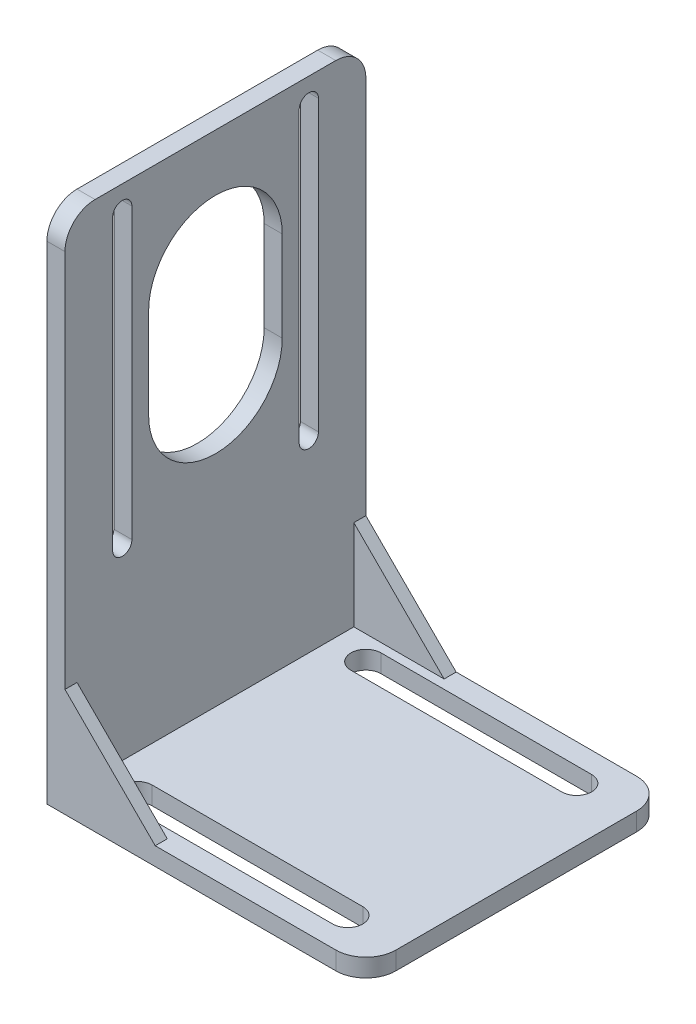
SolidWorks part; units mm, degrees
ref_plane "前视基准面" through (0, 0, 0) normal (0, 0, 1) x (1, 0, 0)
ref_plane "上视基准面" through (0, 0, 0) normal (0, 1, 0) x (1, 0, 0)
ref_plane "右视基准面" through (0, 0, 0) normal (1, 0, 0) x (0, 0, -1)
sketch "草图1" plane through (0, 0, 0) normal (0, 1, 0) x (1, 0, 0)
  line L1 (-26.5, 25) -> (26.5, 25)
  line L2 (-26.5, 25) -> (-26.5, -25)
  line L3 (-26.5, -25) -> (26.5, -25)
  line L4 (26.5, 25) -> (26.5, -25)
  line L5 (-26.5, 25) -> (26.5, -25) construction
  line L6 (-26.5, -25) -> (26.5, 25) construction
  point P0 (0, 0)
  dimension "D1" = 53
  dimension "D2" = 50
extrude "凸台-拉伸1" add sketch "草图1" along normal blind 3
sketch "草图2" plane through (0, 3, 0) normal (0, 1, 0) x (1, 0, 0)
  line L0 (-17.5, 19.0142) -> (17.5, 19.0142) construction
  line L1 (-17.5, 21.5142) -> (17.5, 21.5142)
  line L2 (-17.5, 16.5142) -> (17.5, 16.5142)
  line L3 (0, 0) -> (38.4961, 0) construction
  line L4 (-17.5, -19.0142) -> (17.5, -19.0142) construction
  line L5 (-17.5, -21.5142) -> (17.5, -21.5142)
  line L6 (-17.5, -16.5142) -> (17.5, -16.5142)
  line L7 (-26.5, 25) -> (-26.5, -25) construction
  arc A0 (-17.5, 21.5142) -> (-17.5, 16.5142) centre (-17.5, 19.0142) ccw
  arc A1 (17.5, 16.5142) -> (17.5, 21.5142) centre (17.5, 19.0142) ccw
  arc A2 (-17.5, -21.5142) -> (-17.5, -16.5142) centre (-17.5, -19.0142) cw
  arc A3 (17.5, -16.5142) -> (17.5, -21.5142) centre (17.5, -19.0142) cw
  point P2 (0, 19.0142)
  point P12 (0, -19.0142)
  dimension "D1" = 2.5
  dimension "D2" = 9
  dimension "D3" = 35
extrude "切除-拉伸1" cut sketch "草图2" against normal through all
sketch "草图3" plane through (0, 3, 0) normal (0, 1, 0) x (1, 0, 0)
  line L0 (-26.5, -25) -> (26.5, -25) construction
  line L1 (-26.5, 25) -> (-23.5, 25)
  line L2 (-26.5, 25) -> (-26.5, -25)
  line L3 (-26.5, -25) -> (-23.5, -25)
  line L4 (-23.5, 25) -> (-23.5, -25)
  dimension "D1" = 3
extrude "凸台-拉伸2" add sketch "草图3" along normal blind 83
sketch "草图4" plane through (-26.5, 0, 0) normal (-1, 0, 0) x (0, 0, 1)
  line L0 (-15.5212, 82) -> (-15.5212, 34) construction
  line L1 (-13.9212, 82) -> (-13.9212, 34)
  line L2 (0, 65.5) -> (0, 50.5) construction
  line L3 (11.1, 65.5) -> (11.1, 50.5)
  line L4 (-11.1, 65.5) -> (-11.1, 50.5)
  line L5 (-17.1212, 82) -> (-17.1212, 34)
  line L8 (15.4788, 82) -> (15.4788, 34) construction
  line L11 (17.0788, 82) -> (17.0788, 34)
  line L14 (13.8788, 82) -> (13.8788, 34)
  line L21 (-25, 0) -> (25, 0) construction
  line L22 (0, 58) -> (57.7238, 58) construction
  arc A5 (11.1, 65.5) -> (-11.1, 65.5) centre (0, 65.5) ccw
  arc A6 (-11.1, 50.5) -> (11.1, 50.5) centre (0, 50.5) ccw
  arc A14 (-13.9212, 82) -> (-17.1212, 82) centre (-15.5212, 82) ccw
  arc A15 (-17.1212, 34) -> (-13.9212, 34) centre (-15.5212, 34) ccw
  arc A16 (17.0788, 82) -> (13.8788, 82) centre (15.4788, 82) ccw
  arc A17 (13.8788, 34) -> (17.0788, 34) centre (15.4788, 34) ccw
  point P4 (-15.5212, 58)
  point P6 (0, 58)
  point P16 (15.4788, 58)
  dimension "D1" = 11.1
  dimension "D2" = 15
  dimension "D4" = 1.6
  dimension "D5" = 1.6
  dimension "D3" = 58
  dimension "D6" = 31
  dimension "D7" = 48
  dimension "D8" = 48
  dimension "D9" = 58
extrude "切除-拉伸2" cut sketch "草图4" against normal through all
sketch "草图5" plane through (0, 0, 25) normal (0, 0, 1) x (1, 0, 0)
  line L0 (-23.5, 18) -> (-8.5, 3)
  line L1 (-23.5, 86) -> (-23.5, 3) construction
  line L2 (-23.5, 3) -> (26.5, 3) construction
  line L3 (-23.5, 18) -> (-23.5, 3)
  line L4 (-23.5, 3) -> (-8.5, 3)
  dimension "D1" = 15
  dimension "D2" = 15
extrude "凸台-拉伸3" add sketch "草图5" against normal blind 2
sketch "草图7" plane through (0, 0, -25) normal (0, 0, -1) x (-1, 0, 0)
  line L0 (23.5, 18) -> (8.5, 3)
  line L1 (23.5, 86) -> (23.5, 3) construction
  line L2 (-26.5, 3) -> (23.5, 3) construction
  line L3 (8.5, 3) -> (23.5, 3)
  line L4 (23.5, 3) -> (23.5, 18)
  dimension "D1" = 15
  dimension "D2" = 15
extrude "凸台-拉伸4" add sketch "草图7" against normal blind 2
fillet "圆角1" radius 5 4 edges at (26.5, 1.5, 25) (26.5, 1.5, -25) (-25, 86, 25) (-25, 86, -25)
